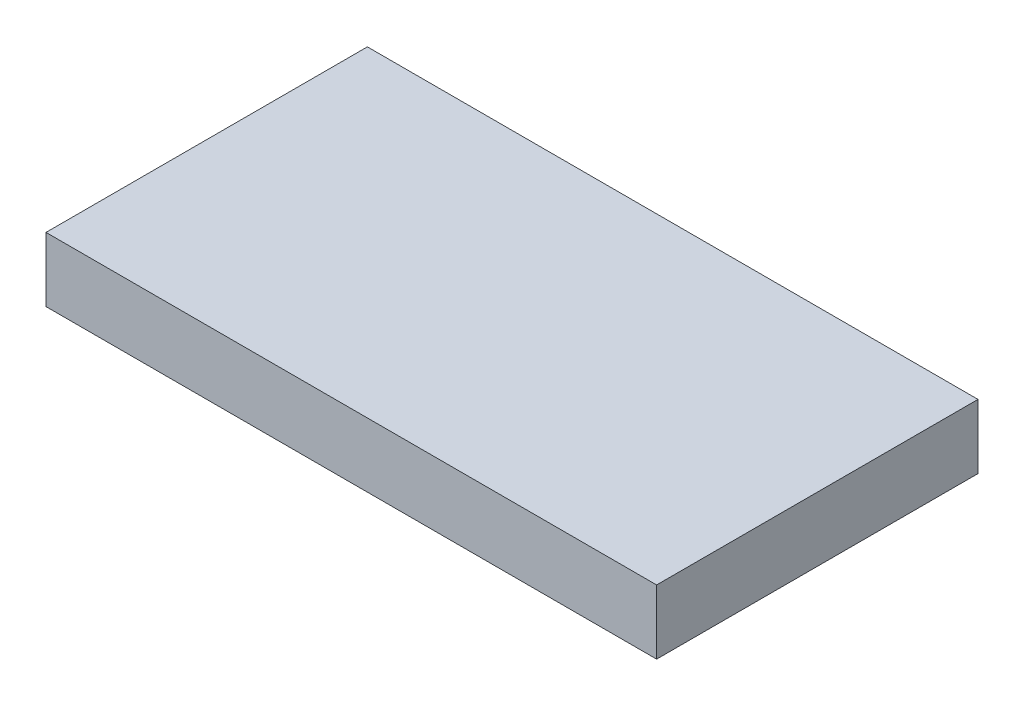
SolidWorks part; units mm, degrees
ref_plane "Front Plane" through (0, 0, 0) normal (0, 0, 1) x (1, 0, 0)
ref_plane "Top Plane" through (0, 0, 0) normal (0, 1, 0) x (1, 0, 0)
ref_plane "Right Plane" through (0, 0, 0) normal (1, 0, 0) x (0, 0, -1)
sketch "Sketch1" plane through (0, 0, 0) normal (0, 1, 0) x (1, 0, 0)
  line L1 (1, 0.5) -> (-0.9, 0.5)
  line L2 (1, 0.5) -> (1, -0.5)
  line L3 (1, -0.5) -> (-0.9, -0.5)
  line L4 (-0.9, 0.5) -> (-0.9, -0.5)
extrude "Boss-Extrude1" add sketch "Sketch1" along normal blind 0.2
